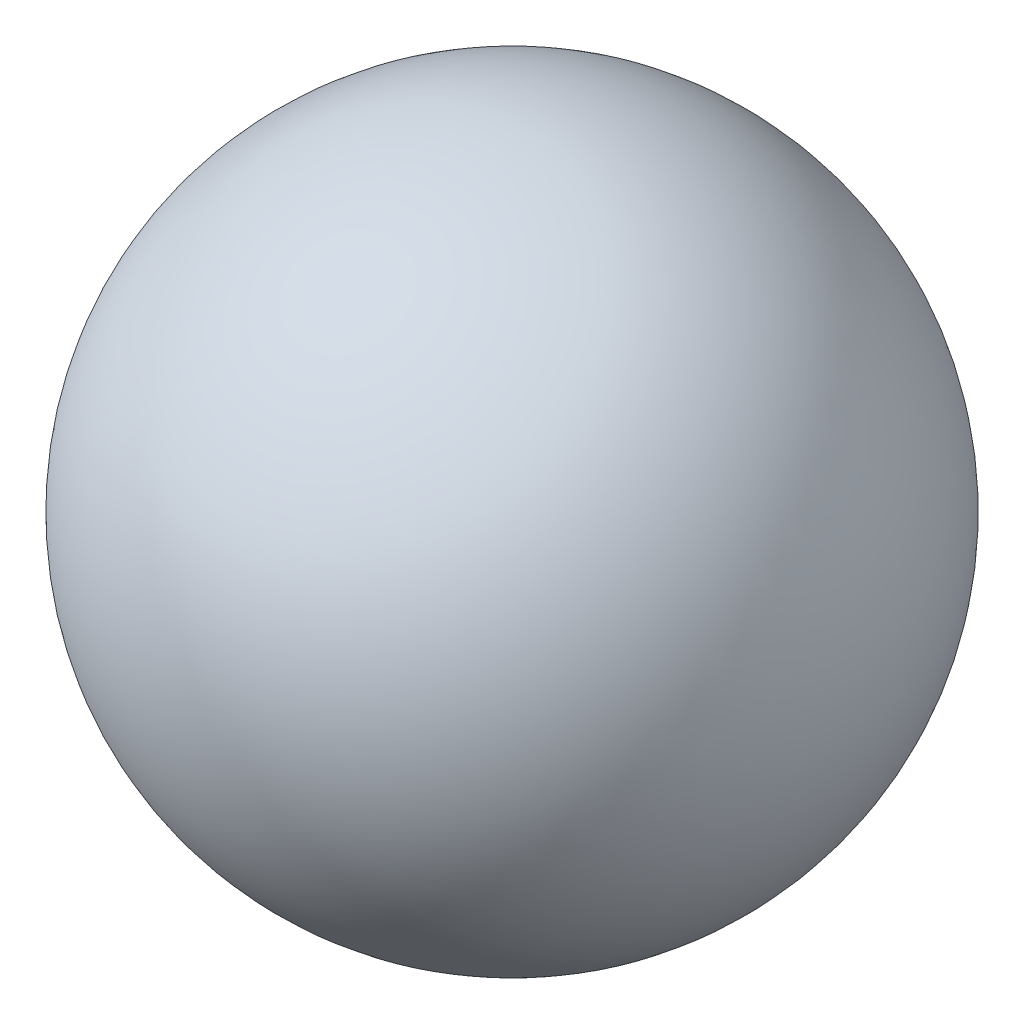
SolidWorks part; units mm, degrees
ref_plane "Front Plane" through (0, 0, 0) normal (0, 0, 1) x (1, 0, 0)
ref_plane "Top Plane" through (0, 0, 0) normal (0, 1, 0) x (1, 0, 0)
ref_plane "Right Plane" through (0, 0, 0) normal (1, 0, 0) x (0, 0, -1)
sketch "Sketch1" plane through (0, 0, 0) normal (1, 0, 0) x (0, 0, -1)
  line L0 (0, -12.7) -> (0, 12.7)
  arc A0 (0, 12.7) -> (0, -12.7) centre (0, 0) cw
  point P4 (0, 0)
  dimension "D1" = 25.4
revolve "Revolve1" add sketch "Sketch1" angle 360 about L0
